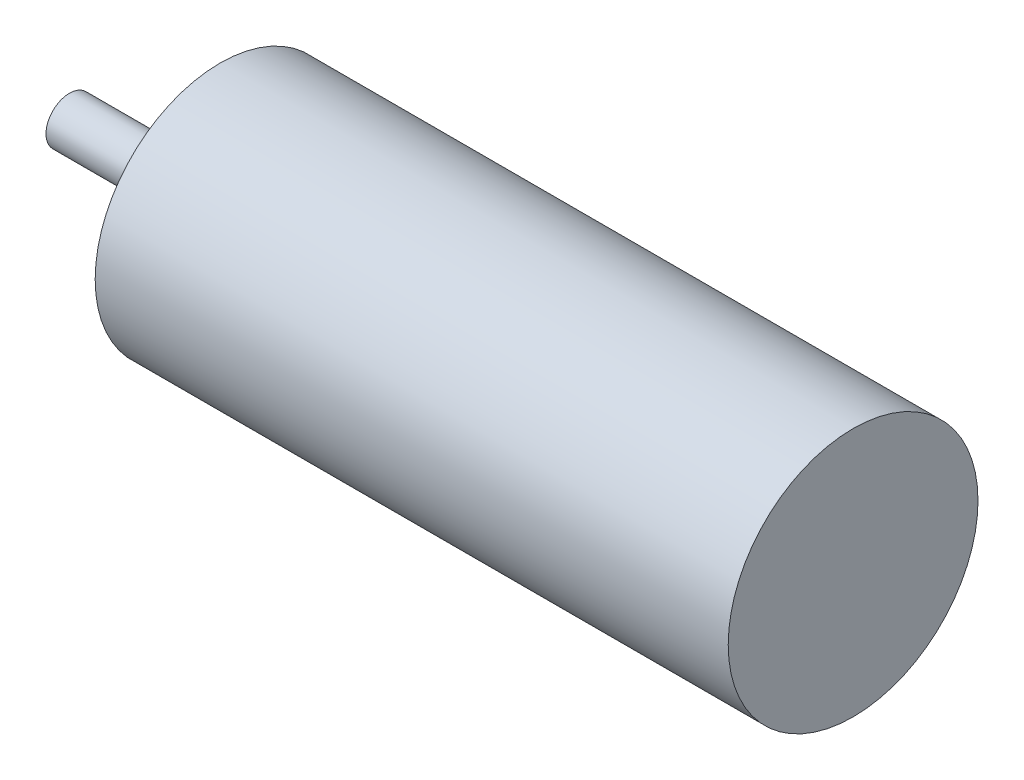
SolidWorks part; units mm, degrees
ref_plane "Front Plane" through (0, 0, 0) normal (0, 0, 1) x (1, 0, 0)
ref_plane "Top Plane" through (0, 0, 0) normal (0, 1, 0) x (1, 0, 0)
ref_plane "Right Plane" through (0, 0, 0) normal (1, 0, 0) x (0, 0, -1)
sketch "Sketch1" plane through (0, 0, 0) normal (0, 0, 1) x (1, 0, 0)
  line L0 (0, 0) -> (100.4, 0)
  line L1 (0, 0) -> (0, 3)
  line L2 (0, 3) -> (15.5, 3)
  line L3 (15.5, 3) -> (15.5, 9)
  line L4 (15.5, 9) -> (19.3, 9)
  line L5 (19.3, 9) -> (19.3, 16)
  line L6 (19.3, 16) -> (100.4, 16)
  line L7 (100.4, 16) -> (100.4, 0)
  dimension "D1" = 100.4
  dimension "D2" = 3
  dimension "D3" = 9
  dimension "D4" = 16
  dimension "D5" = 81.1
  dimension "D6" = 15.5
revolve "Revolve1" add sketch "Sketch1" angle 360 about L0
sketch "Sketch2" plane through (19.3, 0, 0) normal (-1, 0, 0) x (0, 0, 1)
  line L0 (0, 13) -> (0, -13) construction
  line L1 (-13, 0) -> (13, 0) construction
  circle A0 centre (0, 13) radius 1.5
  circle A1 centre (0, -13) radius 1.5
  circle A2 centre (-13, 0) radius 1.5
  circle A3 centre (13, 0) radius 1.5
  point P7 (0, 0)
  dimension "D1" = 26
  dimension "D2" = 3
extrude "Cut-Extrude1" cut sketch "Sketch2" against normal blind 5
